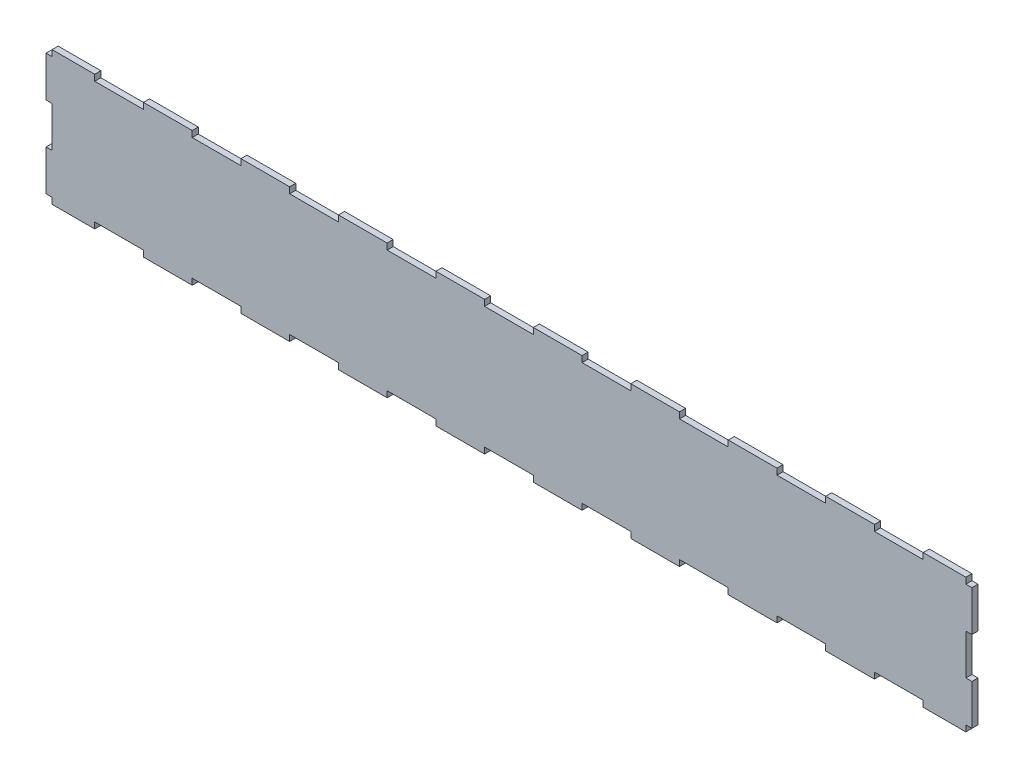
SolidWorks part; units mm, degrees
ref_plane "Front Plane" through (0, 0, 0) normal (0, 0, 1) x (1, 0, 0)
ref_plane "Top Plane" through (0, 0, 0) normal (0, 1, 0) x (1, 0, 0)
ref_plane "Right Plane" through (0, 0, 0) normal (1, 0, 0) x (0, 0, -1)
sketch "Sketch1" plane through (0, 0, 0) normal (0, 0, 1) x (1, 0, 0)
  line L1 (-204, 9) -> (-204, 6)
  line L3 (-180, 6) -> (-180, 9)
  line L5 (-156, 9) -> (-156, 6)
  line L7 (-132, 6) -> (-132, 9)
  line L9 (-108, 9) -> (-108, 6)
  line L11 (-84, 6) -> (-84, 9)
  line L12 (-225, 72) -> (-204, 72)
  line L14 (-60, 9) -> (-60, 6)
  line L16 (-36, 6) -> (-36, 9)
  line L18 (-12, 9) -> (-12, 6)
  line L20 (12, 6) -> (12, 9)
  line L22 (36, 9) -> (36, 6)
  line L24 (60, 6) -> (60, 9)
  line L26 (84, 9) -> (84, 6)
  line L28 (108, 6) -> (108, 9)
  line L30 (132, 9) -> (132, 6)
  line L32 (156, 6) -> (156, 9)
  line L34 (180, 9) -> (180, 6)
  line L36 (204, 6) -> (204, 9)
  line L81 (225, 72) -> (225, 6)
  line L82 (-204, 69) -> (-180, 69)
  line L83 (-225, 72) -> (-225, 6)
  line L85 (-180, 72) -> (-156, 72)
  line L86 (-156, 69) -> (-132, 69)
  line L87 (204, 72) -> (204, 69)
  line L88 (-132, 72) -> (-108, 72)
  line L89 (180, 69) -> (180, 72)
  line L90 (-108, 69) -> (-84, 69)
  line L91 (156, 72) -> (156, 69)
  line L92 (-84, 72) -> (-60, 72)
  line L93 (132, 69) -> (132, 72)
  line L94 (-60, 69) -> (-36, 69)
  line L95 (108, 72) -> (108, 69)
  line L96 (-36, 72) -> (-12, 72)
  line L97 (84, 69) -> (84, 72)
  line L98 (-12, 69) -> (12, 69)
  line L99 (60, 72) -> (60, 69)
  line L100 (12, 72) -> (36, 72)
  line L101 (36, 69) -> (36, 72)
  line L102 (36, 69) -> (60, 69)
  line L103 (12, 72) -> (12, 69)
  line L104 (60, 72) -> (84, 72)
  line L105 (-12, 69) -> (-12, 72)
  line L106 (84, 69) -> (108, 69)
  line L107 (-36, 72) -> (-36, 69)
  line L108 (108, 72) -> (132, 72)
  line L109 (-60, 69) -> (-60, 72)
  line L110 (132, 69) -> (156, 69)
  line L111 (-84, 72) -> (-84, 69)
  line L112 (156, 72) -> (180, 72)
  line L113 (-108, 69) -> (-108, 72)
  line L114 (204, 69) -> (180, 69)
  line L115 (-132, 72) -> (-132, 69)
  line L116 (204, 72) -> (225, 72)
  line L117 (-156, 69) -> (-156, 72)
  line L118 (225, 6) -> (204, 6)
  line L119 (-180, 72) -> (-180, 69)
  line L120 (204, 9) -> (180, 9)
  line L121 (-204, 69) -> (-204, 72)
  line L122 (180, 6) -> (156, 6)
  line L123 (156, 9) -> (132, 9)
  line L124 (132, 6) -> (108, 6)
  line L125 (108, 9) -> (84, 9)
  line L126 (84, 6) -> (60, 6)
  line L127 (60, 9) -> (36, 9)
  line L128 (36, 6) -> (12, 6)
  line L129 (12, 9) -> (-12, 9)
  line L130 (-12, 6) -> (-36, 6)
  line L131 (-36, 9) -> (-60, 9)
  line L132 (-60, 6) -> (-84, 6)
  line L133 (-84, 9) -> (-108, 9)
  line L134 (-108, 6) -> (-132, 6)
  line L135 (-132, 9) -> (-156, 9)
  line L136 (-156, 6) -> (-180, 6)
  line L137 (-180, 9) -> (-204, 9)
  line L138 (-204, 6) -> (-225, 6)
  dimension "D1" = 450
  dimension "D2" = 60
  dimension "D3" = 24
  dimension "D4" = 24
  dimension "D5" = 3
extrude "Boss-Extrude1" add sketch "Sketch1" along normal blind 3
sketch "Sketch3" plane through (0, 0, 3) normal (0, 0, 1) x (1, 0, 0)
  line L1 (-225, 9) -> (-228, 9)
  line L2 (-225, 9) -> (-225, 29)
  line L3 (-225, 29) -> (-228, 29)
  line L4 (-228, 9) -> (-228, 29)
  line L5 (-225, 49) -> (-225, 69)
  line L6 (-225, 49) -> (-228, 49)
  line L7 (-228, 49) -> (-228, 69)
  line L8 (-225, 69) -> (-228, 69)
  line L9 (-225, 49) -> (-225, 29)
  line L10 (228, 9) -> (228, 29)
  line L11 (228, 9) -> (225, 9)
  line L12 (225, 9) -> (225, 29)
  line L13 (228, 29) -> (225, 29)
  line L14 (228, 49) -> (228, 69)
  line L15 (228, 49) -> (225, 49)
  line L16 (225, 49) -> (225, 69)
  line L17 (228, 69) -> (225, 69)
  line L18 (225, 72) -> (225, 6) construction
  line L20 (-225, 72) -> (-225, 6) construction
  line L21 (-225, 72) -> (-204, 72) construction
  line L22 (204, 72) -> (225, 72) construction
  point P7 (-225, 36)
  dimension "D1" = 20
  dimension "D4" = 3
  dimension "D5" = 3
  dimension "D6" = 20
  dimension "D2" = 20
  dimension "D3" = 3
extrude "Boss-Extrude2" add sketch "Sketch3" against normal blind 3 contours L5 L8 L7 L6 | L4 L1 L2 L3 | L14 L17 L16 L15 | L10 L13 L12 L11
